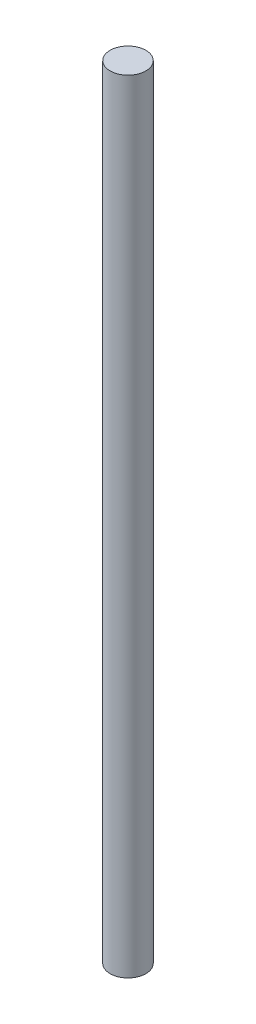
SolidWorks part; units mm, degrees
ref_plane "Alzado" through (0, 0, 0) normal (0, 0, 1) x (1, 0, 0)
ref_plane "Planta" through (0, 0, 0) normal (0, 1, 0) x (1, 0, 0)
ref_plane "Vista lateral" through (0, 0, 0) normal (1, 0, 0) x (0, 0, -1)
sketch "Croquis1" plane through (0, 0, 0) normal (0, 1, 0) x (1, 0, 0)
  circle A0 centre (0, 0) radius 4
  dimension "D1" = 8
extrude "Saliente-Extruir1" add sketch "Croquis1" along normal blind 175
